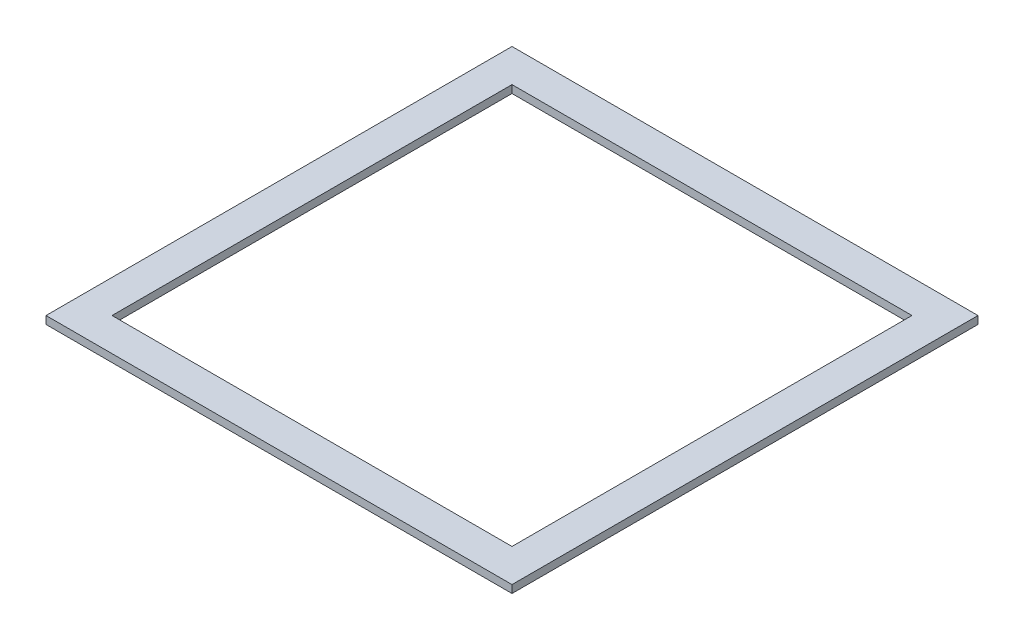
SolidWorks part; units mm, degrees
material "轻木"
ref_plane "前视基准面" through (0, 0, 0) normal (0, 0, 1) x (1, 0, 0)
ref_plane "上视基准面" through (0, 0, 0) normal (0, 1, 0) x (1, 0, 0)
ref_plane "右视基准面" through (0, 0, 0) normal (1, 0, 0) x (0, 0, -1)
sketch "草图1" plane through (0, 0, 0) normal (0, 1, 0) x (1, 0, 0)
  line L1 (-300, 300) -> (300, 300)
  line L2 (-300, 300) -> (-300, -300)
  line L3 (-300, -300) -> (300, -300)
  line L4 (300, 300) -> (300, -300)
  line L5 (0, -300) -> (0, 300) construction
  line L6 (-300, 0) -> (300, 0) construction
  point P0 (0, 0)
  dimension "D1" = 600
extrude "凸台-拉伸1" add sketch "草图1" along normal blind 10
sketch "草图2" plane through (0, 10, 0) normal (0, 1, 0) x (1, 0, 0)
  line L1 (-257.5, 257.5) -> (257.5, 257.5)
  line L2 (-257.5, 257.5) -> (-257.5, -257.5)
  line L3 (-257.5, -257.5) -> (257.5, -257.5)
  line L4 (257.5, 257.5) -> (257.5, -257.5)
  line L5 (0, -257.5) -> (0, 257.5) construction
  line L6 (-257.5, 0) -> (257.5, 0) construction
  point P0 (0, 0)
  dimension "D1" = 515
extrude "切除-拉伸1" cut sketch "草图2" against normal through all
